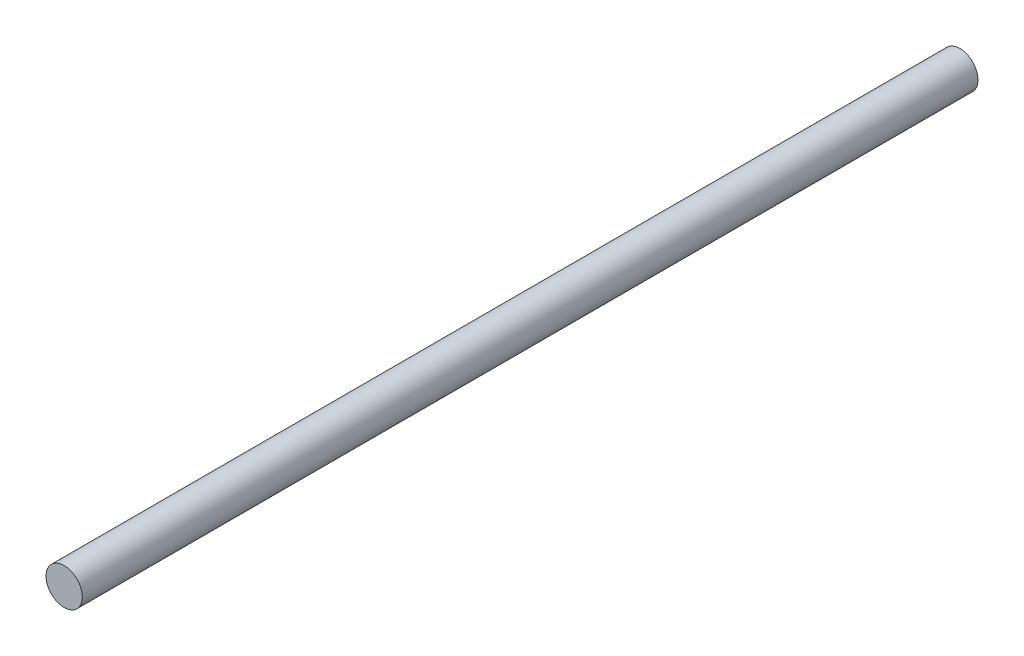
SolidWorks part; units mm, degrees
ref_plane "Front Plane" through (0, 0, 0) normal (0, 0, 1) x (1, 0, 0)
ref_plane "Top Plane" through (0, 0, 0) normal (0, 1, 0) x (1, 0, 0)
ref_plane "Right Plane" through (0, 0, 0) normal (1, 0, 0) x (0, 0, -1)
sketch "Sketch1" plane through (0, 0, 0) normal (0, 0, 1) x (1, 0, 0)
  circle A0 centre (0, 0) radius 1.5 construction
  circle A1 centre (0, 0) radius 1.5
extrude "Boss-Extrude1" add sketch "Sketch1" along normal up to surface (74 mm away)
